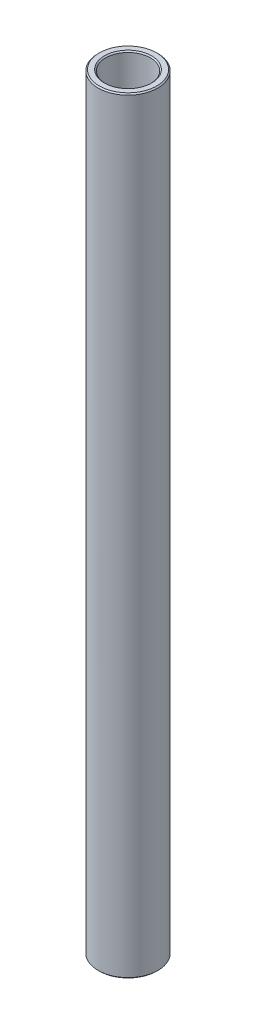
SolidWorks part; units mm, degrees
ref_plane "Front Plane" through (0, 0, 0) normal (0, 0, 1) x (1, 0, 0)
ref_plane "Top Plane" through (0, 0, 0) normal (0, 1, 0) x (1, 0, 0)
ref_plane "Right Plane" through (0, 0, 0) normal (1, 0, 0) x (0, 0, -1)
sketch "Sketch1" plane through (0, 0, 0) normal (0, 0, 1) x (1, 0, 0)
  line L0 (4.7625, 131.7624) -> (4.7625, 294.6112)
  line L1 (4.7625, 294.6112) -> (6.35, 294.6112)
  line L2 (6.35, 294.6112) -> (6.35, 131.7624)
  line L3 (6.35, 131.7624) -> (4.7625, 131.7624)
  line L4 (-10.0875, 140.4936) -> (-120.0875, 140.4936) construction
  line L6 (0, 122.2374) -> (0, 304.1362) construction
  dimension "D1" = 9.525
  dimension "D2" = 9.525
  dimension "D3" = 12.7
  dimension "D4" = 9.525
revolve "Revolve1" add sketch "Sketch1" angle 360 about L6
chamfer "Chamfer1" distance 0.254 angle 45 4 edges at (6.35, 294.6112, 0) (4.7625, 294.6112, 0) (4.7625, 131.7624, 0) (6.35, 131.7624, 0)
equation "\"D4@Sketch1\"=\"D1@Sketch1\""
